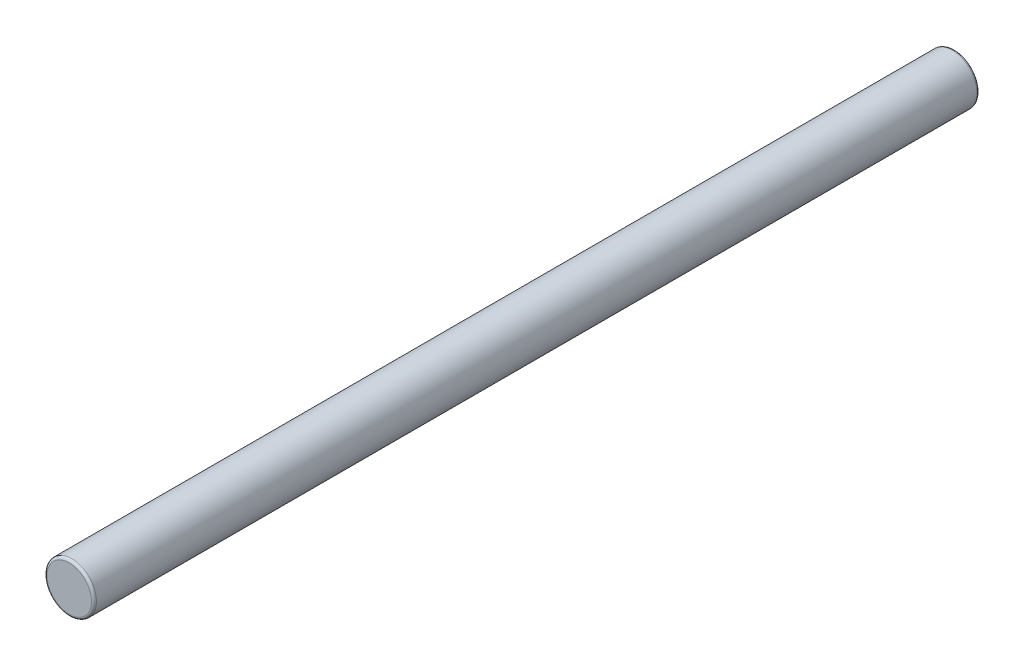
SolidWorks part; units mm, degrees
ref_plane "Front Plane" through (0, 0, 0) normal (0, 0, 1) x (1, 0, 0)
ref_plane "Top Plane" through (0, 0, 0) normal (0, 1, 0) x (1, 0, 0)
ref_plane "Right Plane" through (0, 0, 0) normal (1, 0, 0) x (0, 0, -1)
sketch "Sketch1" plane through (0, 0, 0) normal (0, 0, 1) x (1, 0, 0)
  circle A0 centre (0, 0) radius 0.5
  dimension "D1" = 1
extrude "Boss-Extrude1" add sketch "Sketch1" along normal mid plane 17.9
fillet "Fillet1" radius 0.05 2 edges at (0.5, 0, -8.95) (0.5, 0, 8.95)
